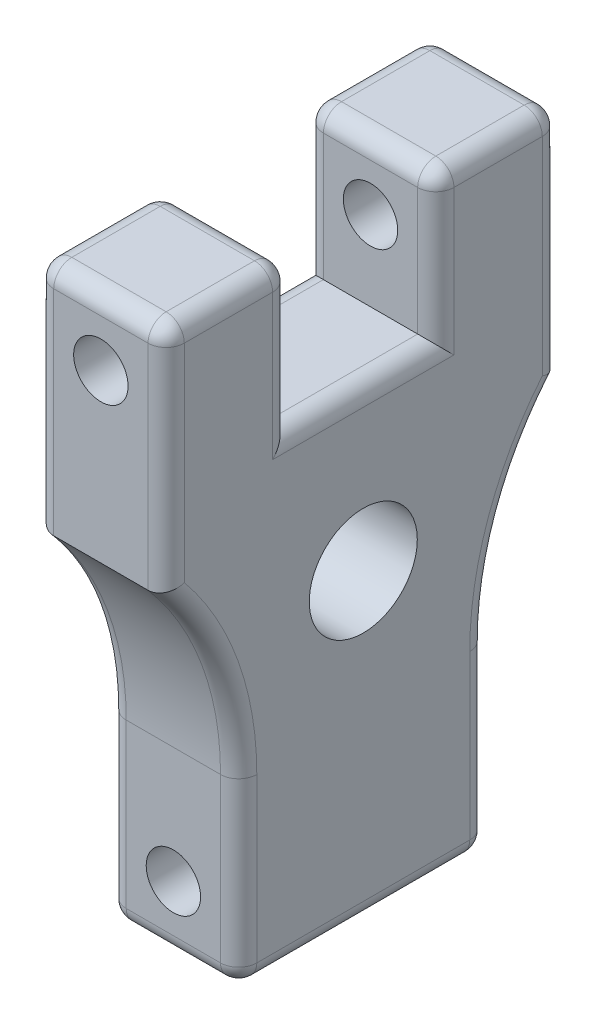
SolidWorks part; units mm, degrees
ref_plane "Front Plane" through (0, 0, 0) normal (0, 0, 1) x (1, 0, 0)
ref_plane "Top Plane" through (0, 0, 0) normal (0, 1, 0) x (1, 0, 0)
ref_plane "Right Plane" through (0, 0, 0) normal (1, 0, 0) x (0, 0, -1)
sketch "Sketch1" plane through (0, 0, 0) normal (1, 0, 0) x (0, 0, -1)
  line L0 (21.8186, 81.28) -> (21.8186, 0) construction
  line L1 (43.6372, 0) -> (43.6372, 31.75)
  line L2 (-12.7, 106.68) -> (9.1186, 106.68)
  line L3 (9.1186, 106.68) -> (9.1186, 81.28)
  line L4 (9.1186, 81.28) -> (34.5186, 81.28)
  line L5 (56.3372, 106.68) -> (56.3372, 66.04)
  line L6 (-12.7, 106.68) -> (-12.7, 66.04)
  line L7 (0, 0) -> (0, 31.75)
  line L8 (34.5186, 106.68) -> (34.5186, 81.28)
  line L9 (56.3372, 106.68) -> (34.5186, 106.68)
  line L11 (43.6372, 0) -> (0, 0)
  arc A0 (-12.7, 66.04) -> (0, 31.75) centre (-52.6415, 31.75) cw
  arc A1 (56.3372, 66.04) -> (43.6372, 31.75) centre (96.2787, 31.75) ccw
  dimension "D1" = 12.7
  dimension "D2" = 69.0372
  dimension "D3" = 25.4
  dimension "D4" = 106.68
  dimension "D5" = 31.75
  dimension "D6" = 40.64
  dimension "D7" = 25.4
extrude "Boss-Extrude1" add sketch "Sketch1" along normal blind 22.86
sketch "Sketch2" plane through (0, 0, 12.7) normal (0, 0, 1) x (1, 0, 0)
  line L0 (22.86, 106.68) -> (0, 106.68) construction
  line L1 (11.43, 106.68) -> (11.43, 95.25) construction
  line L2 (11.43, 95.25) -> (11.43, 11.43) construction
  line L4 (16.1925, 95.25) -> (16.1925, 11.43) construction
  line L5 (11.43, 11.43) -> (11.43, 0) construction
  line L6 (11.43, 95.25) -> (0, 95.25) construction
  line L7 (0, 106.68) -> (0, 66.04) construction
  line L8 (22.86, 0) -> (0, 0) construction
  circle A0 centre (11.43, 95.25) radius 4.7625
  circle A2 centre (11.43, 11.43) radius 4.7625
  dimension "D1" = 83.82
  dimension "D2" = 9.525
extrude "Cut-Extrude1" cut sketch "Sketch2" against normal through all
sketch "Sketch3" plane through (22.86, 0, 0) normal (1, 0, 0) x (0, 0, -1)
  line L0 (21.8186, 53.34) -> (21.8186, 81.28) construction
  line L1 (34.5186, 81.28) -> (9.1186, 81.28) construction
  circle A0 centre (21.8186, 53.34) radius 9.4615
  dimension "D1" = 27.94
  dimension "D2" = 18.923
extrude "Cut-Extrude2" cut sketch "Sketch3" against normal through all
fillet "Fillet1" radius 3.175 30 edges at (11.43, 0, 0) (11.43, 0, -43.6372) (11.43, 106.68, -56.3372) (11.43, 106.68, -34.5186) (11.43, 106.68, -9.1186) (11.43, 106.68, 12.7) (0, 15.875, -43.6372) (0, 50.0331, -46.9142) (0, 86.36, -56.3372) (0, 106.68, -45.4279) (0, 93.98, -34.5186) (0, 81.28, -21.8186) (0, 93.98, -9.1186) (0, 106.68, 1.7907) (0, 86.36, 12.7) (0, 50.0331, 3.277) (0, 15.875, 0) (0, 0, -21.8186) (22.86, 15.875, 0) (22.86, 50.0331, 3.277) (22.86, 86.36, 12.7) (22.86, 106.68, 1.7907) (22.86, 93.98, -9.1186) (22.86, 81.28, -21.8186) (22.86, 93.98, -34.5186) (22.86, 106.68, -45.4279) (22.86, 86.36, -56.3372) (22.86, 50.0331, -46.9142) (22.86, 15.875, -43.6372) (22.86, 0, -21.8186)
